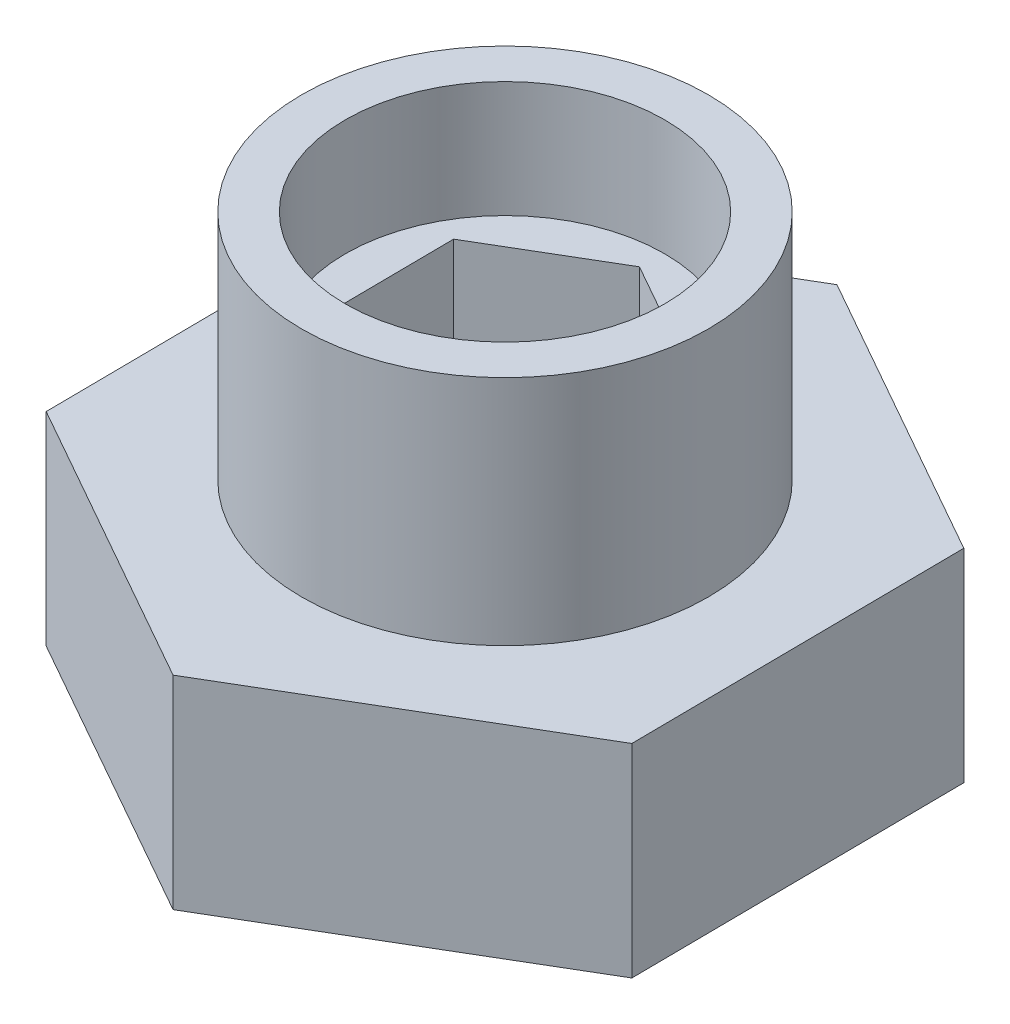
SolidWorks part; units mm, degrees
ref_plane "Front Plane" through (0, 0, 0) normal (0, 0, 1) x (1, 0, 0)
ref_plane "Top Plane" through (0, 0, 0) normal (0, 1, 0) x (1, 0, 0)
ref_plane "Right Plane" through (0, 0, 0) normal (1, 0, 0) x (0, 0, -1)
sketch "Sketch1" plane through (0, 0, 0) normal (0, 1, 0) x (1, 0, 0)
  line L1 (9.946, 5.866) -> (-0.1071, 11.5465)
  line L2 (-0.1071, 11.5465) -> (-10.0531, 5.6805)
  line L3 (-10.0531, 5.6805) -> (-9.946, -5.866)
  line L4 (-9.946, -5.866) -> (0.1071, -11.5465)
  line L5 (0.1071, -11.5465) -> (10.0531, -5.6805)
  line L6 (10.0531, -5.6805) -> (9.946, 5.866)
  circle A0 centre (0, 0) radius 10 construction
  dimension "D1" = 20
extrude "Boss-Extrude1" add sketch "Sketch1" along normal blind 15
sketch "Sketch3" plane through (0, 15, 0) normal (0, 1, 0) x (1, 0, 0)
  circle A0 centre (0, 0) radius 7
  dimension "D1" = 14
extrude "Cut-Extrude1" cut sketch "Sketch3" against normal blind 8 flip side to cut
sketch "Sketch4" plane through (0, 15, 0) normal (0, 1, 0) x (1, 0, 0)
  circle A0 centre (0, 0) radius 5.5
  dimension "D1" = 11
extrude "Cut-Extrude2" cut sketch "Sketch4" against normal blind 4
sketch "Sketch5" plane through (0, 11, 0) normal (0, 1, 0) x (1, 0, 0)
  line L0 (-10.0531, 5.6805) -> (-9.946, -5.866) construction
  line L1 (-4.0715, 2.3006) -> (-4.0281, -2.3757)
  line L2 (-4.0281, -2.3757) -> (0.0434, -4.6763)
  line L3 (0.0434, -4.6763) -> (4.0715, -2.3006)
  line L4 (4.0715, -2.3006) -> (4.0281, 2.3757)
  line L5 (4.0281, 2.3757) -> (-0.0434, 4.6763)
  line L6 (-0.0434, 4.6763) -> (-4.0715, 2.3006)
  circle A0 centre (0, 0) radius 4.6765 construction
  dimension "D1" = 8.1
extrude "Cut-Extrude3" cut sketch "Sketch5" against normal blind 4
sketch "Sketch6" plane through (0, 7, 0) normal (0, 1, 0) x (1, 0, 0)
  circle A0 centre (0, 0) radius 3
  dimension "D1" = 6
extrude "Cut-Extrude4" cut sketch "Sketch6" against normal through all
